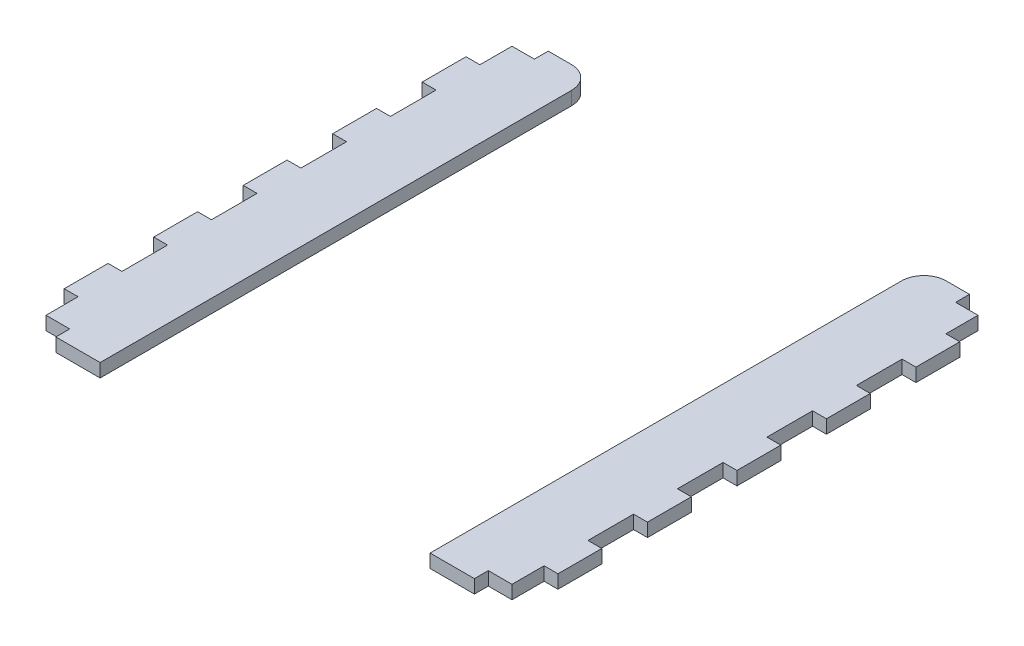
SolidWorks part; units mm, degrees
ref_plane "Front Plane" through (0, 0, 0) normal (0, 0, 1) x (1, 0, 0)
ref_plane "Top Plane" through (0, 0, 0) normal (0, 1, 0) x (1, 0, 0)
ref_plane "Right Plane" through (0, 0, 0) normal (1, 0, 0) x (0, 0, -1)
sketch "Sketch1" plane through (0, 0, 0) normal (0, 1, 0) x (1, 0, 0)
  line L0 (0, 0) -> (0, 21) construction
  line L1 (36.8722, -66.843) -> (55.1722, -66.843) construction
  line L2 (55.1722, 43.5014) -> (55.1722, -66.843) construction
  line L3 (55.1722, 43.5014) -> (36.8722, 43.5014) construction
  line L4 (36.8722, 43.5014) -> (36.8722, -66.843) construction
  line L5 (36.8722, -66.843) -> (55.1722, -66.843)
  line L6 (55.1722, 43.5014) -> (55.1722, -66.843)
  line L7 (55.1722, 43.5014) -> (41.8722, 43.5014)
  line L8 (36.8722, 38.5014) -> (36.8722, -66.843)
  line L9 (-55.1722, 43.5014) -> (-41.8722, 43.5014)
  line L10 (-55.1722, 43.5014) -> (-55.1722, -66.843)
  line L11 (-36.8722, -66.843) -> (-55.1722, -66.843)
  line L12 (-36.8722, 38.5014) -> (-36.8722, -66.843)
  circle A0 centre (0, 0) radius 21 construction
  circle A1 centre (0, 0) radius 21 construction
  arc A2 (-36.8722, 38.5014) -> (-41.8722, 43.5014) centre (-41.8722, 38.5014) ccw
  arc A3 (41.8722, 43.5014) -> (36.8722, 38.5014) centre (41.8722, 38.5014) ccw
  point P16 (-36.8722, 43.5014)
  dimension "D1" = 5
extrude "Boss-Extrude1" add sketch "Sketch1" along normal up to vertex (3 mm away)
sketch "Sketch2" plane through (0, 0, 0) normal (0, 1, 0) x (1, 0, 0)
  line L0 (0, 0) -> (0, 21) construction
  line L1 (0, 0) -> (0, 21) construction
  line L2 (36.8722, 38.5014) -> (36.8722, -66.843) construction
  line L3 (36.8722, 38.5014) -> (36.8722, -66.843) construction
  line L4 (36.8722, -66.843) -> (46.8722, -66.843) construction
  line L5 (46.8722, -66.843) -> (46.8722, -63.843) construction
  line L6 (46.8722, -63.843) -> (36.8722, -63.843) construction
  line L7 (-64.6222, -48.543) -> (-64.6222, -58.543) construction
  line L8 (-52.0722, -56.5708) -> (-52.0722, -63.743)
  line L9 (-55.2722, -56.5708) -> (-52.0722, -56.5708)
  line L10 (-64.2222, 43.5014) -> (-64.2222, 40.5014) construction
  line L11 (46.8722, -66.843) -> (46.8722, -66.943) construction
  line L12 (-52.0722, 3.4292) -> (-55.2722, 3.4292)
  line L13 (-55.2722, 3.4292) -> (-55.2722, -6.7708)
  line L14 (-55.2722, -6.7708) -> (-52.0722, -6.7708)
  line L15 (-52.0722, -6.7708) -> (-52.0722, 3.4292)
  line L16 (-52.0722, 3.4292) -> (-55.2722, 3.4292)
  line L17 (-55.2722, 3.4292) -> (-55.2722, -6.7708)
  line L18 (-55.2722, -6.7708) -> (-52.0722, -6.7708)
  line L19 (-52.0722, -6.7708) -> (-52.0722, 3.4292)
  line L20 (-52.0722, 23.4292) -> (-55.2722, 23.4292)
  line L21 (-55.2722, 23.4292) -> (-55.2722, 13.2292)
  line L22 (-55.2722, 13.2292) -> (-52.0722, 13.2292)
  line L23 (-52.0722, 13.2292) -> (-52.0722, 23.4292)
  line L24 (-52.0722, 23.4292) -> (-55.2722, 23.4292)
  line L25 (-55.2722, 23.4292) -> (-55.2722, 13.2292)
  line L26 (-55.2722, 13.2292) -> (-52.0722, 13.2292)
  line L27 (-52.0722, 13.2292) -> (-52.0722, 23.4292)
  line L28 (46.8722, -65.343) -> (46.7722, -65.343) construction
  line L29 (-55.2722, -66.943) -> (-55.2722, -56.5708)
  line L30 (-46.7722, -66.943) -> (-55.2722, -66.943)
  line L31 (-46.7722, -63.743) -> (-46.7722, -66.943)
  line L32 (-52.0722, -63.743) -> (-46.7722, -63.743)
  line L33 (55.1722, 43.5014) -> (41.8722, 43.5014) construction
  line L34 (47.1722, 40.5014) -> (52.1722, 40.5014) construction
  line L35 (47.1722, 40.5014) -> (47.1722, 43.5014) construction
  line L36 (47.1722, 43.5014) -> (52.1722, 43.5014) construction
  line L37 (52.1722, 40.5014) -> (52.1722, 43.5014) construction
  line L38 (52.1722, 40.5014) -> (55.1722, 40.5014) construction
  line L39 (55.1722, 43.5014) -> (55.1722, -66.843) construction
  line L44 (-55.2722, -26.7708) -> (-52.0722, -26.7708)
  line L45 (-52.0722, -26.7708) -> (-52.0722, -16.5708)
  line L46 (-52.0722, -16.5708) -> (-55.2722, -16.5708)
  line L47 (-55.2722, -16.5708) -> (-55.2722, -26.7708)
  line L48 (-55.2722, -26.7708) -> (-52.0722, -26.7708)
  line L49 (-52.0722, -26.7708) -> (-52.0722, -16.5708)
  line L50 (-52.0722, -16.5708) -> (-55.2722, -16.5708)
  line L51 (-55.2722, -16.5708) -> (-55.2722, -26.7708)
  line L52 (-55.2722, -46.7708) -> (-52.0722, -46.7708)
  line L53 (-52.0722, -46.7708) -> (-52.0722, -36.5708)
  line L54 (-52.0722, -36.5708) -> (-55.2722, -36.5708)
  line L55 (-55.2722, -36.5708) -> (-55.2722, -46.7708)
  line L56 (-55.2722, -46.7708) -> (-52.0722, -46.7708)
  line L57 (-52.0722, -46.7708) -> (-52.0722, -36.5708)
  line L58 (-52.0722, -36.5708) -> (-55.2722, -36.5708)
  line L59 (-55.2722, -36.5708) -> (-55.2722, -46.7708)
  line L68 (52.0722, -36.5708) -> (52.0722, -46.7708)
  line L69 (52.0722, -46.7708) -> (55.2722, -46.7708)
  line L70 (55.2722, -46.7708) -> (55.2722, -36.5708)
  line L71 (55.2722, -36.5708) -> (52.0722, -36.5708)
  line L72 (52.0722, -36.5708) -> (52.0722, -46.7708)
  line L73 (52.0722, -46.7708) -> (55.2722, -46.7708)
  line L74 (55.2722, -46.7708) -> (55.2722, -36.5708)
  line L75 (55.2722, -36.5708) -> (52.0722, -36.5708)
  line L76 (52.0722, -16.5708) -> (52.0722, -26.7708)
  line L77 (52.0722, -26.7708) -> (55.2722, -26.7708)
  line L78 (55.2722, -26.7708) -> (55.2722, -16.5708)
  line L79 (55.2722, -16.5708) -> (52.0722, -16.5708)
  line L80 (52.0722, -16.5708) -> (52.0722, -26.7708)
  line L81 (52.0722, -26.7708) -> (55.2722, -26.7708)
  line L82 (55.2722, -26.7708) -> (55.2722, -16.5708)
  line L83 (55.2722, -16.5708) -> (52.0722, -16.5708)
  line L84 (55.2722, 23.4292) -> (52.0722, 23.4292)
  line L85 (52.0722, 23.4292) -> (52.0722, 13.2292)
  line L86 (52.0722, -63.743) -> (44.9, -63.743)
  line L87 (44.9, -63.743) -> (44.9, -66.943)
  line L88 (44.9, -66.943) -> (55.2722, -66.943)
  line L89 (55.2722, -66.943) -> (55.2722, -56.5708)
  line L90 (55.2722, -56.5708) -> (52.0722, -56.5708)
  line L91 (52.0722, -56.5708) -> (52.0722, -63.743)
  line L92 (52.0722, -63.743) -> (46.7722, -63.743)
  line L93 (46.7722, -63.743) -> (46.7722, -66.943)
  line L94 (46.7722, -66.943) -> (55.2722, -66.943)
  line L95 (55.2722, -66.943) -> (55.2722, -56.5708)
  line L96 (55.2722, -56.5708) -> (52.0722, -56.5708)
  line L97 (52.0722, -56.5708) -> (52.0722, -63.743)
  line L98 (52.0722, 13.2292) -> (55.2722, 13.2292)
  line L99 (55.2722, 13.2292) -> (55.2722, 23.4292)
  line L100 (55.2722, 23.4292) -> (52.0722, 23.4292)
  line L101 (52.0722, 23.4292) -> (52.0722, 13.2292)
  line L102 (52.0722, 13.2292) -> (55.2722, 13.2292)
  line L103 (55.2722, 13.2292) -> (55.2722, 23.4292)
  line L112 (52.0722, 40.6014) -> (52.0722, 33.2292)
  line L113 (55.2722, 40.6014) -> (52.0722, 40.6014)
  line L114 (55.2722, 33.2292) -> (55.2722, 40.6014)
  line L115 (52.0722, 33.2292) -> (55.2722, 33.2292)
  line L116 (52.0722, 40.4014) -> (52.0722, 33.2292)
  line L117 (55.2722, 43.6014) -> (47.0722, 43.6014)
  line L118 (55.2722, 33.2292) -> (55.2722, 43.6014)
  line L119 (52.0722, 33.2292) -> (55.2722, 33.2292)
  line L120 (52.0722, -6.7708) -> (55.2722, -6.7708)
  line L121 (52.0722, 3.4292) -> (52.0722, -6.7708)
  line L122 (55.2722, 3.4292) -> (52.0722, 3.4292)
  line L123 (55.2722, -6.7708) -> (55.2722, 3.4292)
  line L124 (52.0722, -6.7708) -> (55.2722, -6.7708)
  line L125 (52.0722, 3.4292) -> (52.0722, -6.7708)
  line L126 (55.2722, 3.4292) -> (52.0722, 3.4292)
  line L127 (55.2722, -6.7708) -> (55.2722, 3.4292)
  line L150 (52.0722, 40.4014) -> (47.0722, 40.4014)
  line L151 (47.0722, 40.4014) -> (47.0722, 43.6014)
  line L152 (47.1722, 40.5014) -> (47.1722, 40.4014) construction
  line L153 (47.1722, 40.5014) -> (47.0722, 40.5014) construction
  line L154 (47.1722, 43.5014) -> (47.1722, 43.6014) construction
  line L155 (55.1722, 43.5014) -> (55.2722, 43.5014) construction
  line L156 (-52.0722, 33.2292) -> (-55.2722, 33.2292)
  line L157 (-52.0722, 40.4014) -> (-52.0722, 33.2292)
  line L158 (-52.0722, 40.4014) -> (-47.0722, 40.4014)
  line L159 (-47.0722, 40.4014) -> (-47.0722, 43.6014)
  line L160 (-55.2722, 43.6014) -> (-47.0722, 43.6014)
  line L161 (-55.2722, 33.2292) -> (-55.2722, 43.6014)
  dimension "D4" = 5
  dimension "D2" = 0
  dimension "D3" = 0
  dimension "D6" = 0
  dimension "D7" = 0
  dimension "D9" = 0
  dimension "D10" = 0
  dimension "D11" = 0
  dimension "D12" = 0
  dimension "D14" = 0
  dimension "D15" = 0
extrude "Cut-Extrude1" cut sketch "Sketch2" along normal through all
